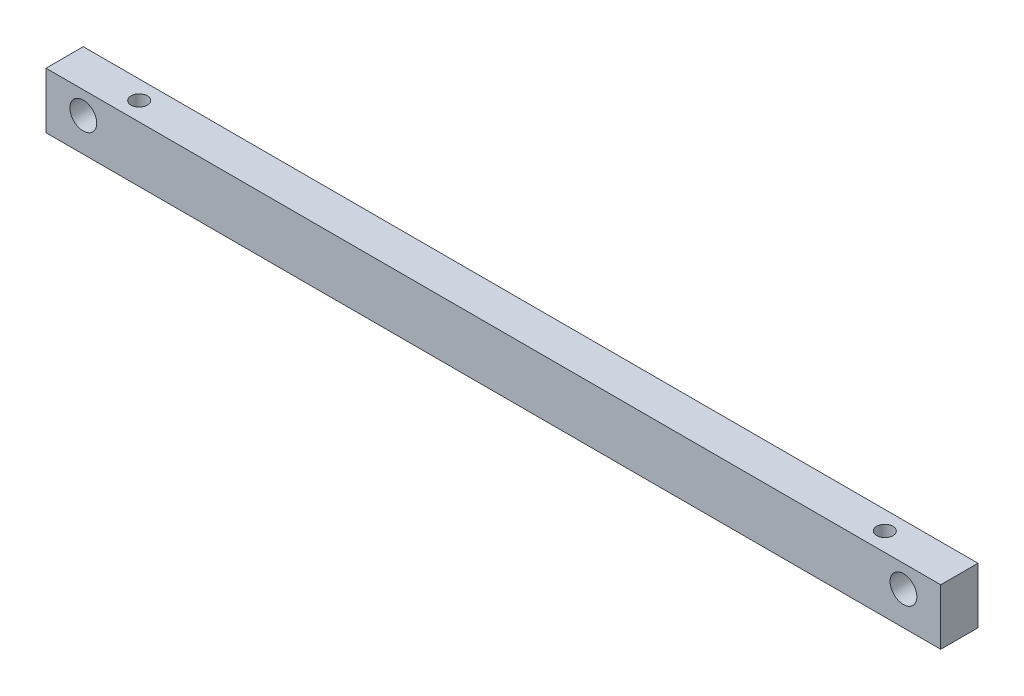
SolidWorks part; units mm, degrees
material "Delrin 2700 NC010, Low Viscosity Acetal Copolymer (SS)"
ref_plane "Front Plane" through (0, 0, 0) normal (0, 0, 1) x (1, 0, 0)
ref_plane "Top Plane" through (0, 0, 0) normal (0, 1, 0) x (1, 0, 0)
ref_plane "Right Plane" through (0, 0, 0) normal (1, 0, 0) x (0, 0, -1)
sketch "Sketch1" plane through (0, 0, 0) normal (1, 0, 0) x (0, 0, -1)
  line L1 (-6.35, 9.525) -> (6.35, 9.525)
  line L2 (-6.35, 9.525) -> (-6.35, -9.525)
  line L3 (-6.35, -9.525) -> (6.35, -9.525)
  line L4 (6.35, 9.525) -> (6.35, -9.525)
  line L5 (-6.35, 9.525) -> (6.35, -9.525) construction
  line L6 (-6.35, -9.525) -> (6.35, 9.525) construction
  point P0 (0, 0)
  dimension "D1" = 12.7
  dimension "D2" = 19.05
extrude "Boss-Extrude1" add sketch "Sketch1" along normal mid plane 304.8
sketch "Sketch2" plane through (0, 0, 6.35) normal (0, 0, 1) x (1, 0, 0)
  line L0 (0, 23.6878) -> (0, -30.5) construction
  line L1 (-152.4, 9.525) -> (-152.4, -9.525) construction
  line L2 (152.4, 9.525) -> (-152.4, 9.525) construction
  circle A0 centre (139.7, 1.905) radius 4.5641
  circle A1 centre (-139.7, 1.905) radius 4.5641
  point P5 (0, 0)
  point P8 (0, 0)
  point P9 (0, 0)
  dimension "D1" = 9.1281
  dimension "D2" = 12.7
  dimension "D3" = 7.62
extrude "Cut-Extrude1" cut sketch "Sketch2" against normal through all both and the other way through all
sketch "Sketch6" plane through (0, 9.525, 0) normal (0, 1, 0) x (1, 0, 0)
  line L0 (0, 29.571) -> (0, -57.1294) construction
  line L1 (-152.4, 6.35) -> (-152.4, -6.35) construction
  circle A0 centre (-127, 0) radius 2.7781
  circle A1 centre (127, 0) radius 2.7781
  dimension "D1" = 5.5562
  dimension "D2" = 25.4
extrude "Cut-Extrude4" cut sketch "Sketch6" against normal through all both and the other way through all
sketch "Sketch8" [suppressed] plane through (0, -9.525, 0) normal (0, -1, 0) x (1, 0, 0)
  line L0 (0, 16.7148) -> (0, -44.4433) construction
  circle A0 centre (-63.5, 0) radius 2.7781
  circle A1 centre (63.5, 0) radius 2.7781
  dimension "D1" = 5.5562
  dimension "D2" = 127
extrude "Cut-Extrude6" [suppressed] cut sketch "Sketch8" against normal through all both and the other way through all
sketch "Sketch9" [suppressed] plane through (0, 9.525, 0) normal (0, 1, 0) x (1, 0, 0)
  line L4 (-152.4, 6.35) -> (-152.4, -6.35)
  line L5 (-152.4, -6.35) -> (152.4, -6.35)
  line L6 (152.4, -6.35) -> (152.4, 6.35)
  line L7 (152.4, 6.35) -> (-152.4, 6.35)
  line L8 (-152.4, 6.35) -> (-152.4, -6.35)
  line L9 (-152.4, -6.35) -> (152.4, -6.35)
  line L10 (152.4, -6.35) -> (152.4, 6.35)
  line L11 (152.4, 6.35) -> (-152.4, 6.35)
  circle A0 centre (-63.5, 0) radius 2.7781
  circle A1 centre (-63.5, 0) radius 2.7781 construction
  circle A2 centre (63.5, 0) radius 2.7781
  circle A3 centre (63.5, 0) radius 2.7781 construction
  dimension "D1" = 0
extrude "Boss-Extrude2" [suppressed] add sketch "Sketch9" along normal blind 19.05
sketch "Sketch7" [suppressed] plane through (0, 0, 6.35) normal (0, 0, 1) x (1, 0, 0)
  line L0 (0, 23.9709) -> (0, -47.8122) construction
  line L1 (152.4, -9.525) -> (-152.4, -9.525) construction
  circle A0 centre (-114.3, 22.225) radius 2.7781
  circle A1 centre (114.3, 22.225) radius 2.7781
  circle A2 centre (0, 22.225) radius 2.7781
  dimension "D1" = 5.5562
  dimension "D2" = 228.6
  dimension "D3" = 31.75
extrude "Cut-Extrude5" [suppressed] cut sketch "Sketch7" against normal through all both and the other way through all
